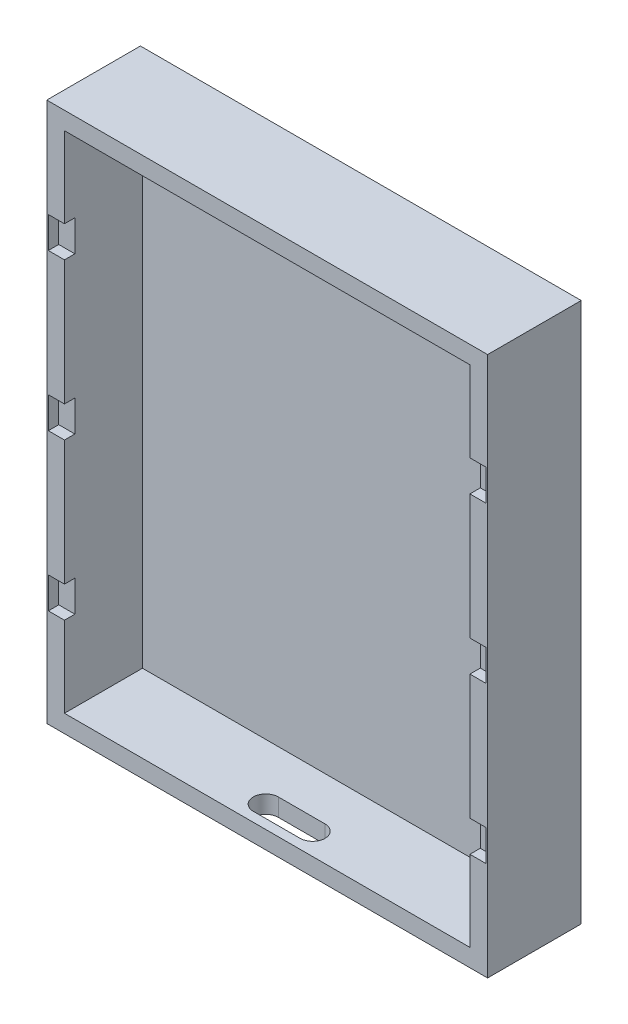
SolidWorks part; units mm, degrees
ref_plane "前视基准面" through (0, 0, 0) normal (0, 0, 1) x (1, 0, 0)
ref_plane "上视基准面" through (0, 0, 0) normal (0, 1, 0) x (1, 0, 0)
ref_plane "右视基准面" through (0, 0, 0) normal (1, 0, 0) x (0, 0, -1)
other "Configuration Table"
sketch "Model" plane through (0, 0, 0) normal (0, 0, 1) x (1, 0, 0)
  line L0 (-4.1804, 99.7831) -> (80.569, 99.7831)
  line L1 (80.569, -4.0164) -> (80.569, 99.7831)
  line L2 (-4.1804, -4.0164) -> (80.569, -4.0164)
  line L3 (-4.1804, -4.0164) -> (-4.1804, 99.7831)
  line L4 (-0.7804, 96.3831) -> (77.169, 96.3831)
  line L5 (77.169, -0.6164) -> (77.169, 96.3831)
  line L6 (-0.7804, -0.6164) -> (77.169, -0.6164)
  line L7 (-0.7804, -0.6164) -> (-0.7804, 96.3831)
  dimension "D5" = 3.4
extrude "凸台-拉伸2" add sketch "Model" along normal blind 15
sketch "草图1" plane through (0, 0, 0) normal (0, 0, -1) x (-1, 0, 0)
  line L1 (-80.569, 99.7831) -> (4.1803, 99.7831)
  line L2 (-80.569, 99.7831) -> (-80.569, -4.0164)
  line L3 (-80.569, -4.0164) -> (4.1804, -4.0164)
  line L4 (4.1803, 99.7831) -> (4.1804, -4.0164)
extrude "凸台-拉伸3" add sketch "草图1" along normal blind 3
sketch "草图2" plane through (0, 0, 15) normal (0, 0, 1) x (1, 0, 0)
  line L1 (-3.8803, 80.8834) -> (-0.7804, 80.8834)
  line L2 (-3.8803, 80.8834) -> (-3.8803, 74.8834)
  line L3 (-3.8803, 74.8834) -> (-0.7804, 74.8834)
  line L4 (-0.7804, 80.8834) -> (-0.7804, 74.8834)
  line L5 (-3.3803, 80.3834) -> (-0.3803, 80.3834) construction
  line L6 (-3.3803, 75.3834) -> (-3.3803, 80.3834) construction
  line L7 (-0.3803, 75.3834) -> (-3.3803, 75.3834) construction
  line L8 (-0.7804, 96.3831) -> (-0.7804, -0.6164) construction
  line L13 (-3.8803, 50.8834) -> (-0.7803, 50.8834)
  line L14 (-3.8803, 50.8834) -> (-3.8803, 44.8834)
  line L15 (-3.8803, 44.8834) -> (-0.7803, 44.8834)
  line L16 (-0.7803, 50.8834) -> (-0.7803, 44.8834)
  line L21 (-3.8803, 20.8834) -> (-0.7803, 20.8834)
  line L22 (-3.8803, 20.8834) -> (-3.8803, 14.8834)
  line L23 (-3.8803, 14.8834) -> (-0.7803, 14.8834)
  line L24 (-0.7803, 20.8834) -> (-0.7803, 14.8834)
  line L31 (38.1943, 99.7831) -> (38.1943, 96.3831) construction
  line L32 (80.569, 99.7831) -> (-4.1804, 99.7831) construction
  line L33 (77.169, 96.3831) -> (-0.7804, 96.3831) construction
  line L34 (77.169, 20.8834) -> (77.169, 14.8834)
  line L35 (80.269, 14.8834) -> (77.169, 14.8834)
  line L36 (80.269, 20.8834) -> (80.269, 14.8834)
  line L37 (80.269, 20.8834) -> (77.169, 20.8834)
  line L38 (77.169, 50.8834) -> (77.169, 44.8834)
  line L39 (80.269, 44.8834) -> (77.169, 44.8834)
  line L40 (80.269, 50.8834) -> (80.269, 44.8834)
  line L41 (80.269, 50.8834) -> (77.169, 50.8834)
  line L42 (77.169, 80.8834) -> (77.169, 74.8834)
  line L43 (80.269, 74.8834) -> (77.169, 74.8834)
  line L44 (80.269, 80.8834) -> (80.269, 74.8834)
  line L45 (80.269, 80.8834) -> (77.169, 80.8834)
  dimension "D1" = 0.5
  dimension "D2" = 0.5
  dimension "D3" = 0.5
  dimension "D4" = 3
extrude "切除-拉伸1" cut sketch "草图2" against normal blind 2
extrude "切除-拉伸3" cut sketch "草图4" against normal blind 10
sketch "草图4" plane through (0, -7.2164, 0) normal (0, -1, 0) x (1, 0, 0)
  line L0 (-5.3803, 10) -> (81.769, 10) construction
  line L3 (38.1943, 15) -> (38.1943, 27.445) construction
  line L5 (14.7486, 12.652) -> (54.2423, 12.652) construction
  line L8 (38.1943, 12.652) -> (38.1943, 8.888) construction
  line L9 (42.6943, 10.77) -> (33.6943, 10.77)
  line L10 (33.6943, 10.77) -> (42.6943, 10.77) construction
  line L11 (33.6943, 13.17) -> (42.6943, 13.17)
  line L12 (33.6943, 8.37) -> (42.6943, 8.37)
  arc A0 (33.6943, 13.17) -> (33.6943, 8.37) centre (33.6943, 10.77) ccw
  arc A1 (42.6943, 8.37) -> (42.6943, 13.17) centre (42.6943, 10.77) ccw
  point P17 (38.1943, 10.77)
  point P21 (38.1943, 10.77)
